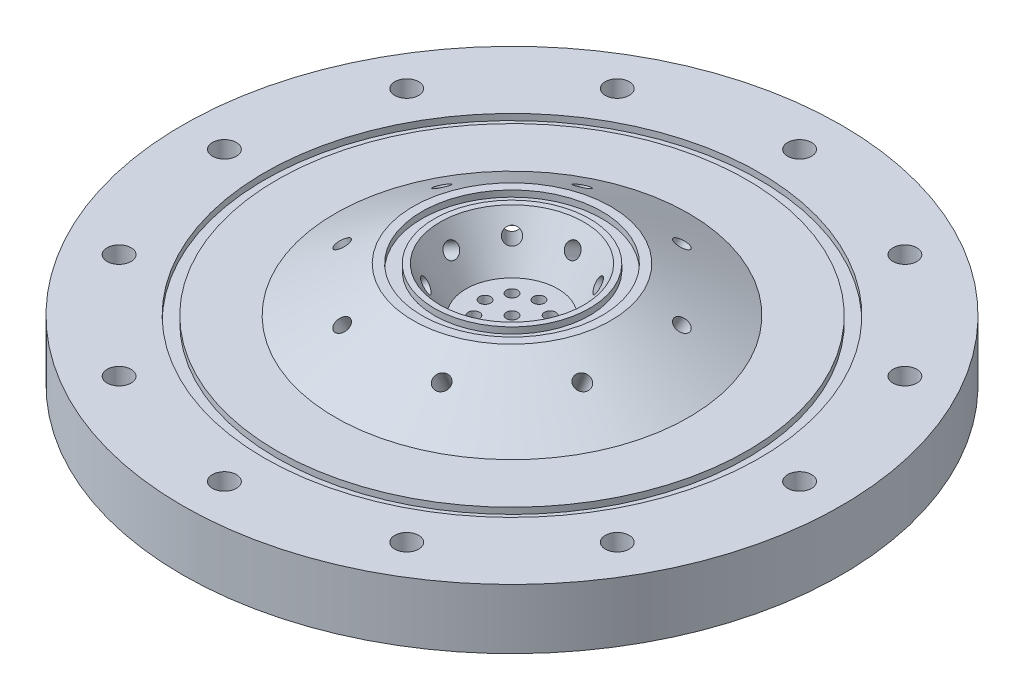
SolidWorks part; units mm, degrees
material "6061-T6 (SS)"
ref_plane "Front Plane" through (0, 0, 0) normal (0, 0, 1) x (1, 0, 0)
ref_plane "Top Plane" through (0, 0, 0) normal (0, 1, 0) x (1, 0, 0)
ref_plane "Right Plane" through (0, 0, 0) normal (1, 0, 0) x (0, 0, -1)
sketch "Sketch1" plane through (0, 0, 0) normal (0, 1, 0) x (1, 0, 0)
  circle A0 centre (0, 0) radius 69.85
  dimension "D1" = 139.7
extrude "Boss-Extrude1" add sketch "Sketch1" along normal blind 12.7
sketch "Sketch2" plane through (0, 12.7, 0) normal (0, 1, 0) x (1, 0, 0)
  circle A0 centre (0, 0) radius 15.24
  circle A1 centre (0, 0) radius 20.955
  dimension "D1" = 30.48
  dimension "D2" = 41.91
extrude "Boss-Extrude2" add sketch "Sketch2" along normal blind 9.525
sketch "Sketch7" plane through (0, 0, 0) normal (0, 0, 1) x (1, 0, 0)
  line L0 (0, 0) -> (0, 22.225) construction
  line L1 (0, 22.225) -> (-15.24, 22.225) construction
  line L2 (15.24, 22.225) -> (-15.24, 22.225) construction
  line L3 (-15.24, 22.225) -> (-15.24, 12.7)
  line L4 (-15.24, 12.7) -> (-9.7407, 12.7)
  line L5 (-15.24, 22.225) -> (-9.7407, 12.7)
  line L7 (-12.9157, 18.1993) -> (-46.927, -1.4372) construction
  line L8 (15.24, 12.7) -> (-15.24, 12.7) construction
  point P11 (0, 0)
  dimension "D1" = 60
  dimension "D2" = 6.35
revolve "Revolve2" add sketch "Sketch7" angle 360 about L0
ref_plane "Plane2" through (0, 0, 0) normal (0.3827, 0, 0.9239) x (0, 1, 0)
sketch "Sketch9" plane through (0, 0, 0) normal (-0.3827, 0, -0.9239) x (-0.9239, 0, 0.3827)
  line L0 (0, 0) -> (0, 22.225) construction
  line L1 (0, 22.225) -> (-20.955, 22.225) construction
  line L2 (20.955, 22.225) -> (-20.955, 22.225) construction
  line L3 (-20.955, 22.225) -> (-20.955, 12.7)
  line L4 (20.955, 12.7) -> (-20.955, 12.7) construction
  line L5 (-20.955, 22.225) -> (-37.4528, 12.7)
  line L6 (-37.4528, 12.7) -> (-20.955, 12.7)
  line L7 (-27.5541, 18.415) -> (-15.6065, -2.2788) construction
  dimension "D1" = 30
  dimension "D2" = 7.62
revolve "Revolve3" add sketch "Sketch9" angle 360 about L0
ref_plane "Plane1" through (-1.8063, -1.0429, 0) normal (-0.866, -0.5, 0) x (0.5, -0.866, 0)
sketch "Sketch13" plane through (0, 0, 0) normal (0, -1, 0) x (1, 0, 0)
  circle A0 centre (0, 0) radius 14.2875
  circle A1 centre (0, 0) radius 25.4
  circle A2 centre (0, 0) radius 33.02
  circle A3 centre (0, 0) radius 41.275
  circle A4 centre (0, 0) radius 7.62
  dimension "D1" = 28.575
  dimension "D2" = 50.8
  dimension "D3" = 66.04
  dimension "D4" = 82.55
  dimension "D5" = 15.24
sketch "Sketch10" plane through (-1.8063, -1.0429, 0) normal (-0.866, -0.5, 0) x (0.5, -0.866, 0)
  circle A0 centre (-22.2189, 0) radius 1.5875
  dimension "D1" = 3.175
extrude "Cut-Extrude5" cut sketch "Sketch10" against normal blind 3.175 and the other way blind 31.496
ref_plane "Plane3" through (13.7311, 25.7425, -5.6876) normal (-0.4619, -0.866, 0.1913) x (0.8001, -0.5, -0.3314)
sketch "Sketch11" plane through (13.7311, 25.7425, -5.6876) normal (-0.4619, -0.866, 0.1913) x (0.8001, -0.5, -0.3314)
  circle A0 centre (14.6551, 0) radius 1.5875
  dimension "D1" = 3.175
extrude "Cut-Extrude6" cut sketch "Sketch11" against normal blind 3.175 and the other way blind 19.05
pattern_circular "CirPattern1" count 8 over 360 about axis through (0, 0, 0) along (0, 1, 0) of "Cut-Extrude6", "Cut-Extrude5"
sketch "Sketch12" plane through (0, 12.7, 0) normal (0, 1, 0) x (1, 0, 0)
  circle A0 centre (0, 0) radius 60.96 construction
  circle A1 centre (60.96, 0) radius 2.54
  dimension "D1" = 121.92
  dimension "D2" = 5.08
extrude "Cut-Extrude7" cut sketch "Sketch12" against normal through all
pattern_circular "CirPattern2" count 12 over 360 about axis through (0, 0, 0) along (0, 1, 0) of "Cut-Extrude7"
extrude "Cut-Extrude10" cut sketch "Sketch13" against normal blind 6.35 contours A3 A2 | A1 A0 | A4
sketch "Sketch15" plane through (0, 12.7, 0) normal (0, 1, 0) x (1, 0, 0)
  circle A0 centre (0, 0) radius 5.715 construction
  circle A1 centre (0, 5.715) radius 1.1906
  dimension "D1" = 2.3813
  dimension "D2" = 11.43
extrude "Cut-Extrude11" cut sketch "Sketch15" against normal through all
pattern_circular "CirPattern3" count 8 over 360 about axis through (0, 0, 0) along (0, 1, 0) of "Cut-Extrude11"
sketch "Sketch16" plane through (0, 0, 0) normal (0, -1, 0) x (1, 0, 0)
  circle A0 centre (0, 0) radius 27.5717
  circle A1 centre (0, 0) radius 30.2133
  dimension "D1" = 2.6416
  dimension "D2" = 60.4266
extrude "Cut-Extrude12" cut sketch "Sketch16" against normal blind 1.3208
sketch "Sketch17" plane through (0, 0, 0) normal (0, -1, 0) x (1, 0, 0)
  circle A0 centre (0, 0) radius 9.3091
  circle A1 centre (0, 0) radius 11.9507
  dimension "D1" = 2.6416
  dimension "D2" = 23.9014
extrude "Cut-Extrude13" cut sketch "Sketch17" against normal blind 1.3208
sketch "Sketch18" plane through (0, 12.7, 0) normal (0, 1, 0) x (1, 0, 0)
  circle A0 centre (0, 0) radius 49.7967
  circle A1 centre (0, 0) radius 52.4383
  dimension "D1" = 2.6416
  dimension "D2" = 104.8766
extrude "Cut-Extrude14" cut sketch "Sketch18" against normal blind 1.3208
sketch "Sketch19" plane through (0, 0, 0) normal (0, -1, 0) x (1, 0, 0)
  circle A0 centre (0, 0) radius 52.4383
  circle A1 centre (0, 0) radius 49.7967
  dimension "D1" = 104.8766
  dimension "D2" = 2.6416
extrude "Cut-Extrude15" cut sketch "Sketch19" against normal blind 1.3208
sketch "Sketch20" plane through (0, 22.225, 0) normal (0, 1, 0) x (1, 0, 0)
  circle A0 centre (0, 0) radius 16.4592
  circle A1 centre (0, 0) radius 19.1008
  dimension "D1" = 38.2016
  dimension "D2" = 2.6416
extrude "Cut-Extrude16" cut sketch "Sketch20" against normal blind 1.3208
sketch "Sketch21" plane through (0, 12.7, 0) normal (0, 1, 0) x (1, 0, 0)
  circle A0 centre (0, 0) radius 1.1906
  circle A1 centre (4.0411, 4.0411) radius 1.1906 construction
extrude "Cut-Extrude17" cut sketch "Sketch21" against normal through all
